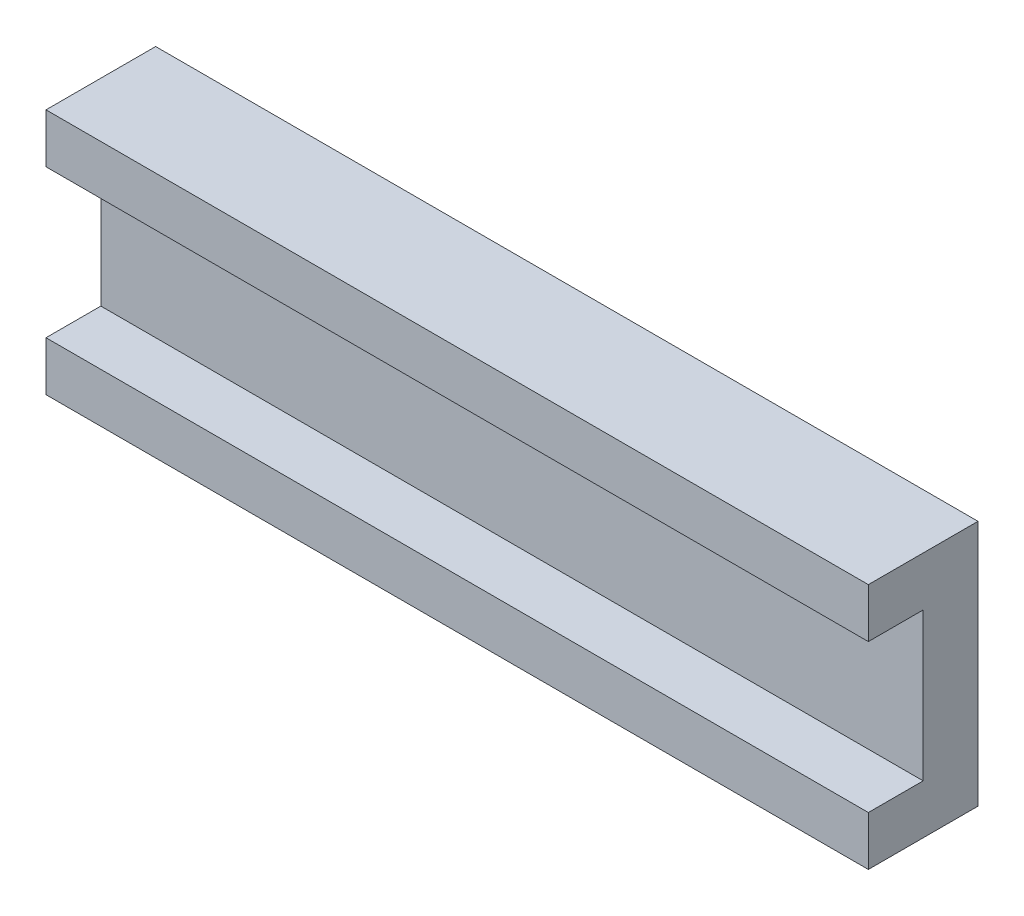
SolidWorks part; units mm, degrees
ref_plane "Front Plane" through (0, 0, 0) normal (0, 0, 1) x (1, 0, 0)
ref_plane "Top Plane" through (0, 0, 0) normal (0, 1, 0) x (1, 0, 0)
ref_plane "Right Plane" through (0, 0, 0) normal (1, 0, 0) x (0, 0, -1)
sketch "Sketch1" plane through (0, 0, 0) normal (0, 0, 1) x (1, 0, 0)
  line L0 (0, 0) -> (-150, 0)
  line L1 (-150, 0) -> (-150, 45)
  line L2 (-150, 45) -> (0, 45)
  line L3 (0, 45) -> (0, 0)
  dimension "D1" = 150
  dimension "D2" = 45
extrude "Boss-Extrude1" add sketch "Sketch1" along normal blind 20
sketch "Sketch2" plane through (0, 0, 20) normal (0, 0, 1) x (1, 0, 0)
  line L0 (0, 36) -> (-150, 36)
  line L1 (0, 0) -> (0, 45) construction
  line L2 (-150, 45) -> (-150, 0) construction
  line L3 (-150, 36) -> (-150, 9)
  line L4 (-150, 9) -> (0, 9)
  line L5 (0, 9) -> (0, 36)
  point P8 (0, 22.5)
  point P9 (0, 22.5)
  dimension "D1" = 27
extrude "Cut-Extrude1" cut sketch "Sketch2" against normal blind 10
